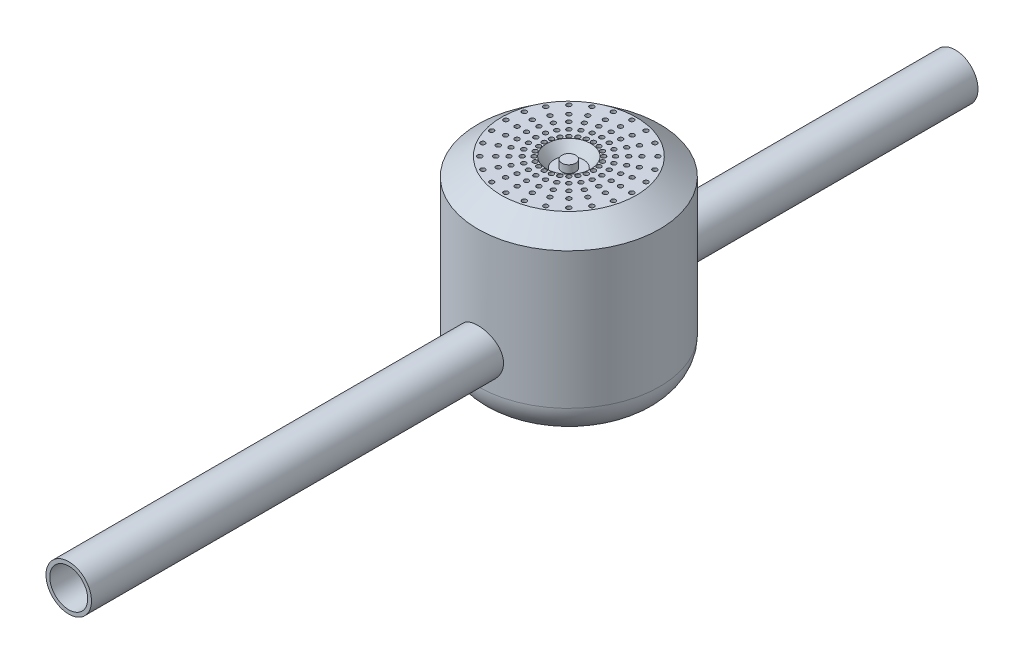
SolidWorks part; units mm, degrees
material "AISI 4340 Steel, annealed"
ref_plane "Front Plane" through (0, 0, 0) normal (0, 0, 1) x (1, 0, 0)
ref_plane "Top Plane" through (0, 0, 0) normal (0, 1, 0) x (1, 0, 0)
ref_plane "Right Plane" through (0, 0, 0) normal (1, 0, 0) x (0, 0, -1)
sketch "Sketch1" plane through (0, 0, 0) normal (0, 1, 0) x (1, 0, 0)
  circle A0 centre (0, 0) radius 6
  dimension "D2" = 12
extrude "Boss-Extrude1" add sketch "Sketch1" along normal blind 8
sketch "Sketch2" plane through (0, 8, 0) normal (0, 1, 0) x (1, 0, 0)
  circle A0 centre (0, 0) radius 4.9983
  dimension "D1" = 9.9965
extrude "Cut-Extrude1" cut sketch "Sketch2" against normal blind 6.5
ref_plane "Plane1" through (0, 0, 5) normal (0, 0, 1) x (1, 0, 0)
sketch "Sketch3" plane through (0, 0, 5) normal (0, 0, 1) x (1, 0, 0)
  circle A0 centre (0, 4) radius 1.5
  circle A1 centre (0, 4) radius 1.25
  dimension "D1" = 3
  dimension "D2" = 2.5
  dimension "D3" = 4
extrude "Boss-Extrude2" add sketch "Sketch3" along normal blind 28
ref_plane "Plane2" through (0, 0, -5.5) normal (0, 0, 1) x (1, 0, 0)
sketch "Sketch4" plane through (0, 0, -5.5) normal (0, 0, 1) x (1, 0, 0)
  circle A0 centre (0, 4) radius 1.5
  dimension "D1" = 3
extrude "Boss-Extrude3" add sketch "Sketch4" against normal blind 20
sketch "Sketch5" plane through (0, 0, 5) normal (0, 0, 1) x (1, 0, 0)
  circle A0 centre (0, 4) radius 1.25
  dimension "D1" = 2.5
extrude "Cut-Extrude2" cut sketch "Sketch5" against normal blind 2
fillet "Fillet2" radius 2 1 edges at (0, 0, 6)
sketch "Sketch6" plane through (0, 0, 5) normal (0, 0, 1) x (1, 0, 0)
  circle A0 centre (0, 4) radius 1.25
  point P3 (0, 0)
  point P4 (0, 0)
  dimension "D1" = 2.5
sketch "Sketch9" plane through (0, 0, 5) normal (0, 0, -1) x (-1, 0, 0)
  circle A0 centre (0, 4) radius 1.25
  dimension "D1" = 2.5
extrude "Cut-Extrude12" cut sketch "Sketch9" against normal blind 30
sketch "Sketch10" plane through (0, 8, 0) normal (0, 1, 0) x (1, 0, 0)
  circle A0 centre (0, 0) radius 5
  circle A1 centre (0, 0) radius 6
  dimension "D1" = 12
  dimension "D2" = 10
extrude "Boss-Extrude4" add sketch "Sketch10" along normal blind 2
sketch "Sketch11" plane through (0, 0, 0) normal (1, 0, 0) x (0, 0, -1)
  line L0 (0, 10) -> (0, -1.705) construction
  line L1 (5, 10) -> (-5, 10) construction
  line L2 (-6, 10) -> (-6, 11)
  line L3 (-6, 11) -> (-4.456, 12.1635)
  line L4 (-4.456, 12.1635) -> (-1.456, 12.1635)
  line L5 (-1.456, 12.1635) -> (-0.956, 11.5)
  line L6 (-0.956, 11.5) -> (-0.456, 11.5)
  line L7 (-0.456, 11.5) -> (-0.456, 12)
  line L8 (-0.456, 12) -> (0, 12)
  line L9 (0, 12) -> (0, 10)
  line L10 (0, 10) -> (-6, 10)
  dimension "D1" = 1
  dimension "D2" = 2
  dimension "D3" = 3
  dimension "D4" = 0.5
  dimension "D5" = 0.5
  dimension "D6" = 0.5
  dimension "D7" = 127
revolve "Revolve1" add sketch "Sketch11" angle 360 about L0
sketch "Sketch12" plane through (0, 12.1635, 0) normal (0, 1, 0) x (1, 0, 0)
  circle A0 centre (0, 4.1551) radius 0.15
  circle A1 centre (0, 3.4092) radius 0.15
  circle A2 centre (0, 2.7931) radius 0.15
  circle A3 centre (0, 2.1769) radius 0.15
  circle A4 centre (0, 1.6256) radius 0.15
  circle A5 centre (1.0754, 4.0135) radius 0.15
  circle A6 centre (0.8824, 3.2931) radius 0.15
  circle A7 centre (0.7229, 2.6979) radius 0.15
  circle A8 centre (0.5634, 2.1027) radius 0.15
  circle A9 centre (0.4207, 1.5702) radius 0.15
  circle A10 centre (2.0776, 3.5984) radius 0.15
  circle A11 centre (1.7046, 2.9525) radius 0.15
  circle A12 centre (1.3965, 2.4189) radius 0.15
  circle A13 centre (1.0884, 1.8852) radius 0.15
  circle A14 centre (0.8128, 1.4078) radius 0.15
  circle A15 centre (2.9381, 2.9381) radius 0.15
  circle A16 centre (2.4107, 2.4107) radius 0.15
  circle A17 centre (1.975, 1.975) radius 0.15
  circle A18 centre (1.5393, 1.5393) radius 0.15
  circle A19 centre (1.1494, 1.1494) radius 0.15
  circle A20 centre (3.5984, 2.0776) radius 0.15
  circle A21 centre (2.9525, 1.7046) radius 0.15
  circle A22 centre (2.4189, 1.3965) radius 0.15
  circle A23 centre (1.8852, 1.0884) radius 0.15
  circle A24 centre (1.4078, 0.8128) radius 0.15
  circle A25 centre (4.0135, 1.0754) radius 0.15
  circle A26 centre (3.2931, 0.8824) radius 0.15
  circle A27 centre (2.6979, 0.7229) radius 0.15
  circle A28 centre (2.1027, 0.5634) radius 0.15
  circle A29 centre (1.5702, 0.4207) radius 0.15
  circle A30 centre (4.1551, 0) radius 0.15
  circle A31 centre (3.4092, 0) radius 0.15
  circle A32 centre (2.7931, 0) radius 0.15
  circle A33 centre (2.1769, 0) radius 0.15
  circle A34 centre (1.6256, 0) radius 0.15
  circle A35 centre (4.0135, -1.0754) radius 0.15
  circle A36 centre (3.2931, -0.8824) radius 0.15
  circle A37 centre (2.6979, -0.7229) radius 0.15
  circle A38 centre (2.1027, -0.5634) radius 0.15
  circle A39 centre (1.5702, -0.4207) radius 0.15
  circle A40 centre (3.5984, -2.0776) radius 0.15
  circle A41 centre (2.9525, -1.7046) radius 0.15
  circle A42 centre (2.4189, -1.3965) radius 0.15
  circle A43 centre (1.8852, -1.0884) radius 0.15
  circle A44 centre (1.4078, -0.8128) radius 0.15
  circle A45 centre (2.9381, -2.9381) radius 0.15
  circle A46 centre (2.4107, -2.4107) radius 0.15
  circle A47 centre (1.975, -1.975) radius 0.15
  circle A48 centre (1.5393, -1.5393) radius 0.15
  circle A49 centre (1.1494, -1.1494) radius 0.15
  circle A50 centre (2.0776, -3.5984) radius 0.15
  circle A51 centre (1.7046, -2.9525) radius 0.15
  circle A52 centre (1.3965, -2.4189) radius 0.15
  circle A53 centre (1.0884, -1.8852) radius 0.15
  circle A54 centre (0.8128, -1.4078) radius 0.15
  circle A55 centre (1.0754, -4.0135) radius 0.15
  circle A56 centre (0.8824, -3.2931) radius 0.15
  circle A57 centre (0.7229, -2.6979) radius 0.15
  circle A58 centre (0.5634, -2.1027) radius 0.15
  circle A59 centre (0.4207, -1.5702) radius 0.15
  circle A60 centre (0, -4.1551) radius 0.15
  circle A61 centre (0, -3.4092) radius 0.15
  circle A62 centre (0, -2.7931) radius 0.15
  circle A63 centre (0, -2.1769) radius 0.15
  circle A64 centre (0, -1.6256) radius 0.15
  circle A65 centre (-1.0754, -4.0135) radius 0.15
  circle A66 centre (-0.8824, -3.2931) radius 0.15
  circle A67 centre (-0.7229, -2.6979) radius 0.15
  circle A68 centre (-0.5634, -2.1027) radius 0.15
  circle A69 centre (-0.4207, -1.5702) radius 0.15
  circle A70 centre (-2.0776, -3.5984) radius 0.15
  circle A71 centre (-1.7046, -2.9525) radius 0.15
  circle A72 centre (-1.3965, -2.4189) radius 0.15
  circle A73 centre (-1.0884, -1.8852) radius 0.15
  circle A74 centre (-0.8128, -1.4078) radius 0.15
  circle A75 centre (-2.9381, -2.9381) radius 0.15
  circle A76 centre (-2.4107, -2.4107) radius 0.15
  circle A77 centre (-1.975, -1.975) radius 0.15
  circle A78 centre (-1.5393, -1.5393) radius 0.15
  circle A79 centre (-1.1494, -1.1494) radius 0.15
  circle A80 centre (-3.5984, -2.0776) radius 0.15
  circle A81 centre (-2.9525, -1.7046) radius 0.15
  circle A82 centre (-2.4189, -1.3965) radius 0.15
  circle A83 centre (-1.8852, -1.0884) radius 0.15
  circle A84 centre (-1.4078, -0.8128) radius 0.15
  circle A85 centre (-4.0135, -1.0754) radius 0.15
  circle A86 centre (-3.2931, -0.8824) radius 0.15
  circle A87 centre (-2.6979, -0.7229) radius 0.15
  circle A88 centre (-2.1027, -0.5634) radius 0.15
  circle A89 centre (-1.5702, -0.4207) radius 0.15
  circle A90 centre (-4.1551, 0) radius 0.15
  circle A91 centre (-3.4092, 0) radius 0.15
  circle A92 centre (-2.7931, 0) radius 0.15
  circle A93 centre (-2.1769, 0) radius 0.15
  circle A94 centre (-1.6256, 0) radius 0.15
  circle A95 centre (-4.0135, 1.0754) radius 0.15
  circle A96 centre (-3.2931, 0.8824) radius 0.15
  circle A97 centre (-2.6979, 0.7229) radius 0.15
  circle A98 centre (-2.1027, 0.5634) radius 0.15
  circle A99 centre (-1.5702, 0.4207) radius 0.15
  circle A100 centre (-3.5984, 2.0776) radius 0.15
  circle A101 centre (-2.9525, 1.7046) radius 0.15
  circle A102 centre (-2.4189, 1.3965) radius 0.15
  circle A103 centre (-1.8852, 1.0884) radius 0.15
  circle A104 centre (-1.4078, 0.8128) radius 0.15
  circle A105 centre (-2.9381, 2.9381) radius 0.15
  circle A106 centre (-2.4107, 2.4107) radius 0.15
  circle A107 centre (-1.975, 1.975) radius 0.15
  circle A108 centre (-1.5393, 1.5393) radius 0.15
  circle A109 centre (-1.1494, 1.1494) radius 0.15
  circle A110 centre (-2.0776, 3.5984) radius 0.15
  circle A111 centre (-1.7046, 2.9525) radius 0.15
  circle A112 centre (-1.3965, 2.4189) radius 0.15
  circle A113 centre (-1.0884, 1.8852) radius 0.15
  circle A114 centre (-0.8128, 1.4078) radius 0.15
  circle A115 centre (-1.0754, 4.0135) radius 0.15
  circle A116 centre (-0.8824, 3.2931) radius 0.15
  circle A117 centre (-0.7229, 2.6979) radius 0.15
  circle A118 centre (-0.5634, 2.1027) radius 0.15
  circle A119 centre (-0.4207, 1.5702) radius 0.15
  circle A120 centre (0, 0) radius 4.456 construction
  point P0 (0, 4.1551)
  point P1 (0, 3.4092)
  point P2 (0, 2.7931)
  point P3 (0, 2.1769)
  point P4 (0, 1.6256)
  point P247 (0, 0)
  dimension "D1" = 0.3
  dimension "D2" = 24
extrude "Cut-Extrude13" cut sketch "Sketch12" against normal blind 5
